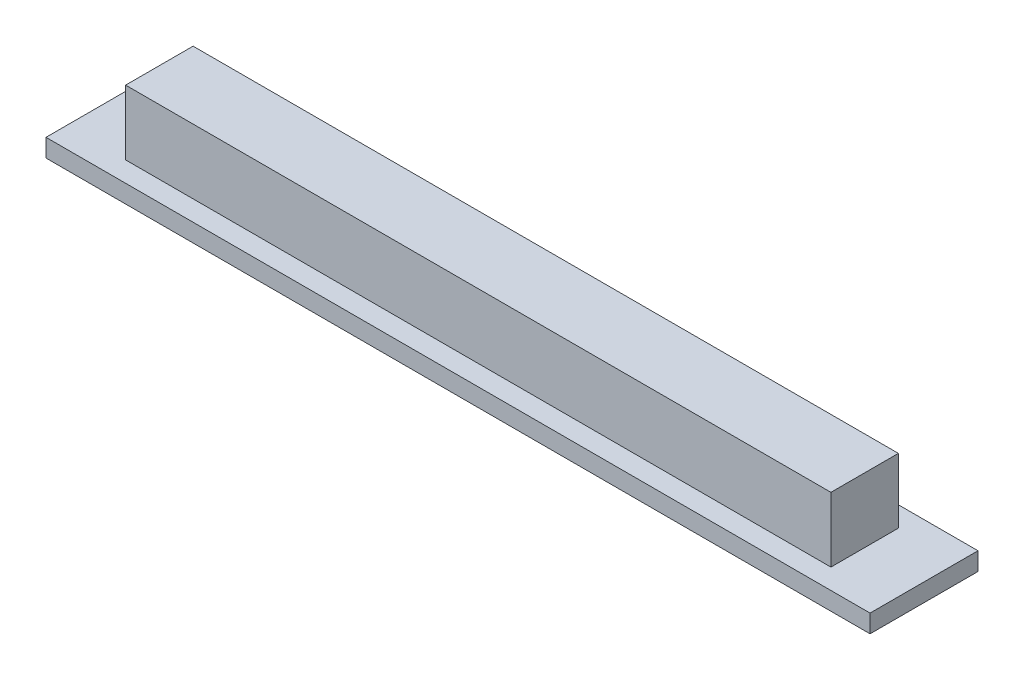
SolidWorks part; units mm, degrees
material "普通碳钢"
ref_plane "前视基准面" through (0, 0, 0) normal (0, 0, 1) x (1, 0, 0)
ref_plane "上视基准面" through (0, 0, 0) normal (0, 1, 0) x (1, 0, 0)
ref_plane "右视基准面" through (0, 0, 0) normal (1, 0, 0) x (0, 0, -1)
sketch "草图1" plane through (0, 0, 0) normal (0, 1, 0) x (1, 0, 0)
  line L1 (-22.9, 3) -> (22.9, 3)
  line L2 (-22.9, 3) -> (-22.9, -3)
  line L3 (-22.9, -3) -> (22.9, -3)
  line L4 (22.9, 3) -> (22.9, -3)
  line L5 (-22.9, 3) -> (22.9, -3) construction
  line L6 (-22.9, -3) -> (22.9, 3) construction
  point P0 (0, 0)
  dimension "D1" = 6
  dimension "D2" = 45.8
extrude "凸台-拉伸1" add sketch "草图1" along normal blind 1
sketch "草图2" plane through (0, 1, 0) normal (0, 1, 0) x (1, 0, 0)
  line L1 (-19.6, 1.875) -> (19.6, 1.875)
  line L2 (-19.6, 1.875) -> (-19.6, -1.875)
  line L3 (-19.6, -1.875) -> (19.6, -1.875)
  line L4 (19.6, 1.875) -> (19.6, -1.875)
  line L5 (-19.6, 1.875) -> (19.6, -1.875) construction
  line L6 (-19.6, -1.875) -> (19.6, 1.875) construction
  point P0 (0, 0)
  dimension "D1" = 3.75
  dimension "D2" = 39.2
extrude "凸台-拉伸2" add sketch "草图2" along normal blind 3.6 contours L1 L4 L3 L2
